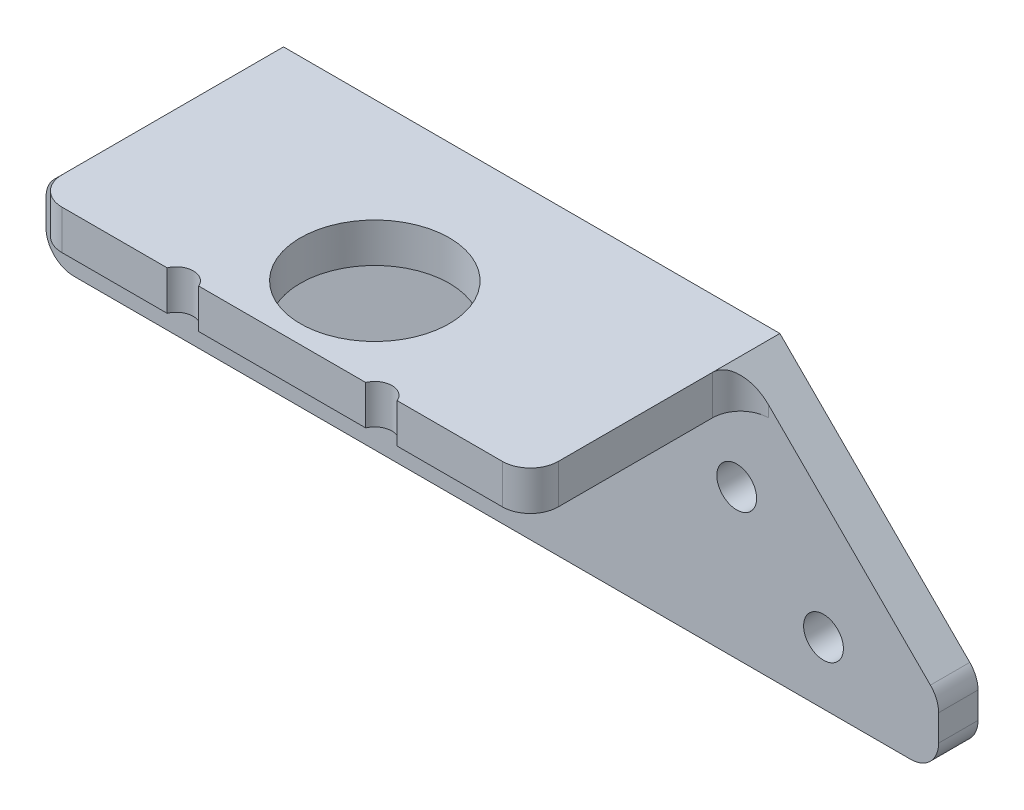
SolidWorks part; units mm, degrees
other "Markup1"
sketch "Sketch16" plane through (-39.1905, -20.3674, 24.05) normal (-0.0308, -0.9994, 0.0158) x (0.9994, -0.0306, 0.0156)
material "Alloy Steel"
ref_plane "Front Plane" through (0, 0, 0) normal (0, 0, 1) x (1, 0, 0)
ref_plane "Top Plane" through (0, 0, 0) normal (0, 1, 0) x (1, 0, 0)
ref_plane "Right Plane" through (0, 0, 0) normal (1, 0, 0) x (0, 0, -1)
ref_plane "Plane1" through (0, 0, 5) normal (0, 0, 1) x (1, 0, 0)
sketch "Sketch1" plane through (0, 0, 5) normal (0, 0, 1) x (1, 0, 0)
  line L0 (-21.1834, 0) -> (-21.1834, -8.8135)
  line L1 (-19.5308, -15.2763) -> (24.6825, -15.2763)
  line L2 (24.6825, -14.2126) -> (23.7179, 0)
  line L3 (23.7179, 0) -> (23.7179, 4.989)
  line L4 (23.7179, 4.989) -> (-21.1834, 4.989)
  line L5 (-21.1834, 4.989) -> (-21.1834, 0)
  arc A0 (-21.1834, -8.8135) -> (-19.5308, -15.2763) centre (-19.5308, -11.8336) ccw
  arc A1 (24.6825, -15.2763) -> (24.6825, -14.2126) centre (24.6825, -14.7444) ccw
  dimension "D1" = 44.9013
extrude "Boss-Extrude1" add sketch "Sketch1" against normal blind 3.5719
sketch "Sketch2" plane through (0, 0, 5) normal (0, 0, 1) x (1, 0, 0)
  line L0 (23.77, 0) -> (-21.23, 0)
  line L1 (-21.23, 0) -> (-21.23, 3.5719)
  line L2 (-21.23, 3.5719) -> (23.77, 3.5719)
  line L3 (23.77, 3.5719) -> (23.77, 0)
  dimension "D1" = 3.5719
extrude "Boss-Extrude2" add sketch "Sketch2" along normal blind 19.05
hole_wizard "Ø5.0 (5) Diameter Hole1" [suppressed] positions "Sketch4" profile "Sketch3" hole size "Ø5.0" standard "ANSI Metric"
sketch "Sketch4" plane through (0, 0, 1.4281) normal (0, 0, -1) x (-1, 0, 0)
  point P0 (-20.42, -22.057)
  point P1 (20.42, -22.057)
sketch "Sketch3" plane through (20.42, -22.057, 1.4281) normal (1, 0, 0) x (0, 1, 0)
  line L0 (0, 0) -> (0, 22.6219)
  line L1 (0, 22.6219) -> (2.5, 22.6219)
  line L2 (2.5, 22.6219) -> (2.5, 0)
  line L5 (2.5, 0) -> (0, 0)
  line L11 (0, -6.35) -> (0, 107.95) construction
  dimension "Thru Hole Dia." = 5
  dimension "Thru Hole Depth" = 22.6219
fillet "Fillet1" radius 2 1 edges at (1.2672, 4.989, 1.4281)
fillet "Fillet2" [suppressed] radius 8
hole_wizard "Ø13.5 (13.5) Diameter Hole1" [suppressed] positions "Sketch6" profile "Sketch5" hole size "Ø13.5" standard "ANSI Metric"
sketch "Sketch6" plane through (0, 4.989, 0) normal (0, 1, 0) x (1, 0, 0)
  line L0 (-55, -5) -> (55, -5) construction
  point P0 (0, -13)
  dimension "D1" = 8
sketch "Sketch5" plane through (0, 4.989, 13) normal (1, 0, 0) x (0, 0, 1)
  line L0 (0, 0) -> (0, 20.2653)
  line L1 (0, 20.2653) -> (6.75, 20.2653)
  line L2 (6.75, 20.2653) -> (6.75, 0)
  line L5 (6.75, 0) -> (0, 0)
  line L11 (0, -6.35) -> (0, 107.95) construction
  dimension "Thru Hole Dia." = 13.5
  dimension "Thru Hole Depth" = 20.2653
hole_wizard "Ø5.0 (5) Diameter Hole2" [suppressed] positions "Sketch8" profile "Sketch7" hole size "Ø5.0" standard "ANSI Metric"
sketch "Sketch8" plane through (0, 4.989, 0) normal (0, 1, 0) x (1, 0, 0)
  line L0 (-55, -5) -> (55, -5) construction
  point P0 (-12, -17.51)
  point P1 (12, -17.51)
  dimension "D1" = 12.51
  dimension "D2" = 12.51
  dimension "D3" = 12
  dimension "D4" = 24
sketch "Sketch7" plane through (-12, 4.989, 17.51) normal (1, 0, 0) x (0, 0, 1)
  line L0 (0, 0) -> (0, 20.2653)
  line L1 (0, 20.2653) -> (2.5, 20.2653)
  line L2 (2.5, 20.2653) -> (2.5, 0)
  line L5 (2.5, 0) -> (0, 0)
  line L11 (0, -6.35) -> (0, 107.95) construction
  dimension "Thru Hole Dia." = 5
  dimension "Thru Hole Depth" = 20.2653
sketch "Sketch9" plane through (0, 0, 5) normal (0, 0, 1) x (1, 0, 0)
  line L1 (-21.1834, 3.5719) -> (23.7179, 3.5719)
  line L2 (-21.1834, 3.5719) -> (-21.1834, 4.989)
  line L3 (-21.1834, 4.989) -> (23.7179, 4.989)
  line L4 (23.7179, 3.5719) -> (23.7179, 4.989)
extrude "Cut-Extrude1" cut sketch "Sketch9" against normal blind 10
sketch "Sketch10" plane through (0, 0, 5) normal (0, 0, 1) x (1, 0, 0)
  line L0 (29.4905, -16.975) -> (14.2053, -1.6897) construction
  line L1 (-21.1834, 0) -> (23.7179, 0) construction
  line L2 (-25.6987, -15.2653) -> (-15.0019, -4.5684) construction
  circle A0 centre (21.6238, -9.1082) radius 1.8034
  circle A1 centre (-19.0029, -8.5694) radius 1.8034
  circle A2 centre (29.4905, -16.975) radius 1.8714
  circle A3 centre (-25.6987, -15.2653) radius 1.7313
  dimension "D1" = 3.6068
  dimension "D2" = 3.6068
  dimension "D3" = 135
  dimension "D4" = 11.1252
  dimension "D5" = 135
  dimension "D6" = 29.3487
extrude "Cut-Extrude2" [suppressed] cut sketch "Sketch10" against normal through all
sketch "Sketch11" plane through (0, 0, 5) normal (0, 0, 1) x (1, 0, 0)
  line L0 (-19.5308, -15.2763) -> (24.6825, -15.2763) construction
  line L1 (-8.1008, -15.2763) -> (10.9492, -15.2763)
  line L2 (-8.1008, -15.2763) -> (-8.1008, -7.3607)
  line L3 (-8.1008, -7.3607) -> (10.9492, -7.3607)
  line L4 (10.9492, -15.2763) -> (10.9492, -7.3607)
  dimension "D1" = 19.05
  dimension "D2" = 11.43
extrude "Cut-Extrude3" [suppressed] cut sketch "Sketch11" against normal through all
sketch "Sketch13" plane through (0, 0, 5) normal (0, 0, 1) x (1, 0, 0)
  line L4 (-21.23, 3.5719) -> (-39.1905, -14.3886)
  line L5 (23.77, 3.5719) -> (41.7305, -14.3886)
  line L6 (-39.1905, -14.3886) -> (-39.1905, -20.3674)
  line L8 (23.77, 0) -> (23.77, 3.5719)
  line L9 (23.77, 3.5719) -> (-21.23, 3.5719)
  line L10 (-21.23, 3.5719) -> (-21.23, 0)
  line L11 (-21.23, 0) -> (23.77, 0)
  line L13 (23.77, 3.5719) -> (-21.23, 3.5719)
  line L19 (-39.1905, -20.3674) -> (41.7305, -20.3674)
  line L20 (41.7305, -20.3674) -> (41.7305, -14.3886)
  dimension "D1" = 135
  dimension "D2" = 135
  dimension "D3" = 25.4
  dimension "D4" = 0
extrude "Boss-Extrude3" add sketch "Sketch13" against normal through all
sketch "Sketch14" plane through (0, 0, 5) normal (0, 0, 1) x (1, 0, 0)
  line L2 (-21.23, 3.5719) -> (-39.1905, -14.3886) construction
  line L3 (-28.7554, -14.7299) -> (-34.1436, -9.3417) construction
  line L4 (41.7305, -14.3886) -> (23.77, 3.5719) construction
  line L5 (31.2955, -14.7299) -> (36.6836, -9.3417) construction
  circle A0 centre (-28.7554, -14.7299) radius 1.8034
  circle A1 centre (-20.8887, -6.8632) radius 1.8034
  circle A2 centre (23.4288, -6.8632) radius 1.8034
  circle A3 centre (31.2955, -14.7299) radius 1.8034
  dimension "D1" = 7.62
  dimension "D5" = 3.6068
  dimension "D6" = 3.6068
  dimension "D8" = 3.6068
  dimension "D9" = 3.6068
  dimension "D2" = 7.1374
  dimension "D3" = 11.1252
  dimension "D4" = 7.62
  dimension "D7" = 7.62
  dimension "D10" = 11.1252
  dimension "D11" = 7.1374
extrude "Cut-Extrude4" cut sketch "Sketch14" against normal through all
fillet "Fillet3" radius 2.54 8 edges at (23.77, 1.7859, 24.05) (-21.23, 1.7859, 24.05) (-21.23, 1.7859, 5) (23.77, 1.7859, 5) (-39.1905, -14.3886, 3.2141) (-39.1905, -20.3674, 3.2141) (41.7305, -14.3886, 3.2141) (41.7305, -20.3674, 3.2141)
sketch "Sketch15" plane through (0, 0, 0) normal (0, -1, 0) x (1, 0, 0)
  line L0 (-21.23, 14.525) -> (23.77, 14.525) construction
  line L3 (-21.23, 21.51) -> (-21.23, 7.54) construction
  line L4 (23.77, 21.51) -> (23.77, 7.54) construction
  line L5 (-36.6505, 1.4281) -> (39.1905, 1.4281) construction
  circle A0 centre (1.27, 15.6521) radius 6.75
  circle A1 centre (-7.73, 24.6521) radius 1.55
  circle A2 centre (10.27, 24.6521) radius 1.55
  point P5 (-21.23, 14.525)
  point P9 (1.27, 14.525)
  dimension "D1" = 13.5
  dimension "D2" = 3.1
  dimension "D3" = 3.1
  dimension "D4" = 9
  dimension "D5" = 9
  dimension "D6" = 18
  dimension "D7" = 14.224
extrude "Cut-Extrude5" cut sketch "Sketch15" against normal through all and the other way through all
